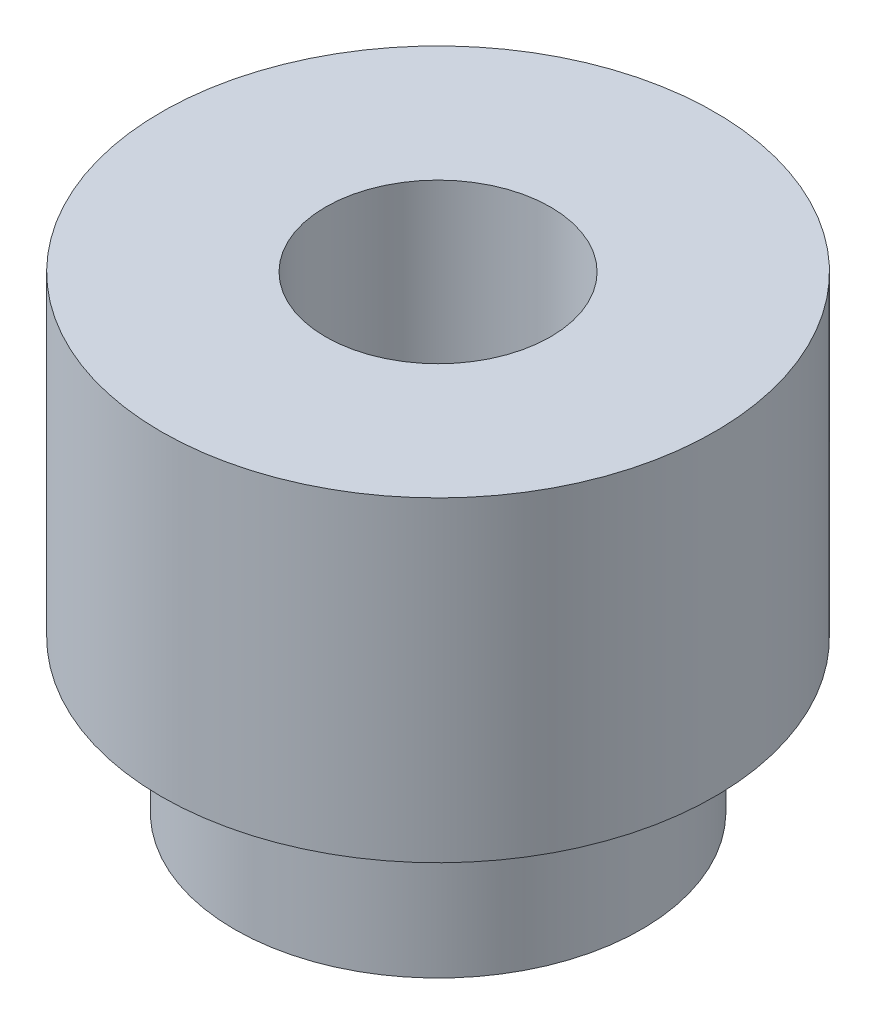
SolidWorks part; units mm, degrees
ref_plane "Front Plane" through (0, 0, 0) normal (0, 0, 1) x (1, 0, 0)
ref_plane "Top Plane" through (0, 0, 0) normal (0, 1, 0) x (1, 0, 0)
ref_plane "Right Plane" through (0, 0, 0) normal (1, 0, 0) x (0, 0, -1)
sketch "Sketch1" plane through (0, 0, 0) normal (0, 1, 0) x (1, 0, 0)
  circle A0 centre (0, 0) radius 2.045
  dimension "D1" = 4.09
extrude "Boss-Extrude1" add sketch "Sketch1" along normal blind 1.524
sketch "Sketch2" plane through (0, 1.524, 0) normal (0, 1, 0) x (1, 0, 0)
  circle A0 centre (0, 0) radius 2.7813
  dimension "D1" = 5.5626
extrude "Boss-Extrude2" add sketch "Sketch2" along normal blind 3.175
hole_wizard "#4-40 Tapped Hole1" positions "Sketch6" profile "Sketch7" tap size "#4-40" standard "ANSI Inch"
sketch "Sketch6" plane through (0, 4.699, 0) normal (0, 1, 0) x (1, 0, 0)
  point P0 (0, 0)
sketch "Sketch7" plane through (0, 4.699, 0) normal (1, 0, 0) x (0, 0, 1)
  line L0 (0, 0) -> (0, 8.2992)
  line L1 (0, 8.2992) -> (1.1303, 7.62)
  line L2 (1.1303, 7.62) -> (1.1303, 0)
  line L5 (1.1303, 0) -> (0, 0)
  line L10 (0, 8.2992) -> (-1.1303, 7.62) construction
  line L11 (0, -6.35) -> (0, 107.95) construction
  dimension "Tap Drill Dia." = 2.2606
  dimension "Tap Drill Depth" = 7.62
  dimension "Drill Angle" = 118
cosmetic thread "Hole Thread1" parameters "D1"=5.588, "D2"=2.8448
